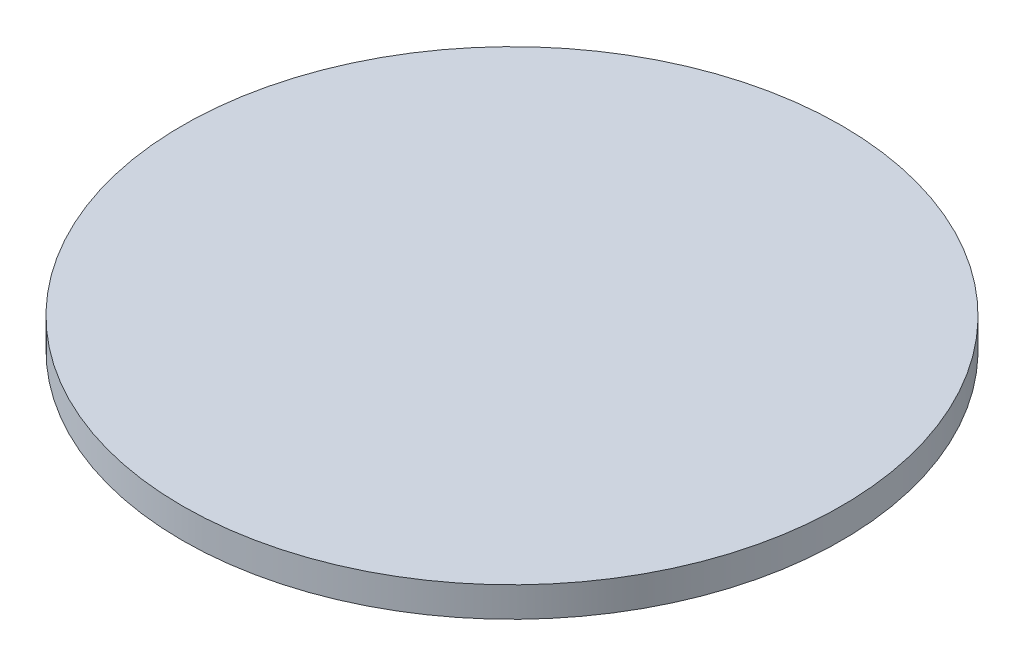
SolidWorks part; units mm, degrees
ref_plane "Front Plane" through (0, 0, 0) normal (0, 0, 1) x (1, 0, 0)
ref_plane "Top Plane" through (0, 0, 0) normal (0, 1, 0) x (1, 0, 0)
ref_plane "Right Plane" through (0, 0, 0) normal (1, 0, 0) x (0, 0, -1)
sketch "Sketch1" plane through (0, 0, 0) normal (0, 1, 0) x (1, 0, 0)
  circle A0 centre (0, 0) radius 35
extrude "Boss-Extrude1" add sketch "Sketch1" along normal blind 3.175
sketch "Sketch2" plane through (0, 3.175, 0) normal (0, 1, 0) x (1, 0, 0)
  line L0 (-31.0825, 16.0896) -> (16.22, 31.0147) construction
  line L1 (-31.0825, 16.0896) -> (-7.4313, 23.5522)
  line L2 (-7.4313, 23.5522) -> (-10.5316, 33.3779)
  circle A0 centre (0, 0) radius 35 construction
  arc A1 (-10.5316, 33.3779) -> (34.1719, -7.5684) centre (0, 0) cw
  arc A2 (-10.5316, 33.3779) -> (-23.6404, -25.8096) centre (0, 0) ccw
  circle A3 centre (0, 0) radius 25
